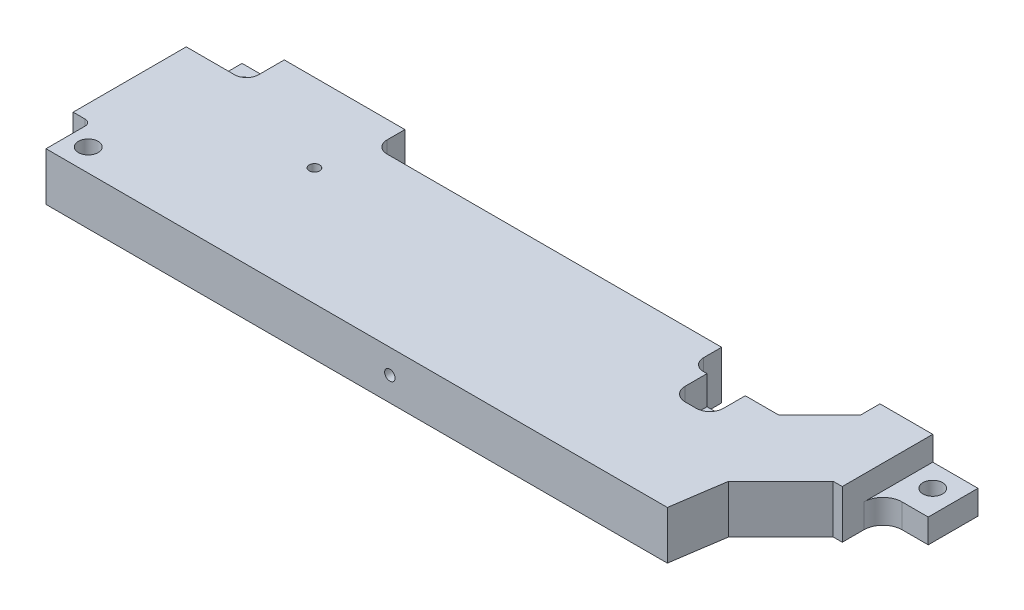
SolidWorks part; units mm, degrees
ref_plane "Front" through (0, 0, 0) normal (0, 0, 1) x (1, 0, 0)
ref_plane "Top" through (0, 0, 0) normal (0, 1, 0) x (1, 0, 0)
ref_plane "Right" through (0, 0, 0) normal (1, 0, 0) x (0, 0, -1)
sketch "Sketch1" plane through (0, 0, 0) normal (0, 0, 1) x (1, 0, 0)
  line L1 (-96.9906, 0) -> (106.1234, 0) construction
  line L2 (250, 8) -> (250, -8)
  line L3 (0, 8) -> (250, 8)
  line L4 (0, 8) -> (0, -8)
  line L5 (0, -8) -> (250, -8)
  dimension "D1" = 16
  dimension "D2" = 250
extrude "Base-Extrude" add sketch "Sketch1" along normal blind 65
sketch "Sketch3" plane through (0, 8, 0) normal (0, 1, 0) x (-1, 0, 0)
  line L0 (-250, 30) -> (-232, 30)
  line L1 (-250, 65) -> (-250, 0) construction
  line L2 (-214.6357, 47.3643) -> (-212, 65)
  line L3 (-250, 65) -> (0, 65) construction
  line L4 (-214.6357, 47.3643) -> (-232, 30)
  point P10 (-232, 30)
  dimension "D3" = 35
  dimension "D4" = 18
  dimension "D1" = 81.5
  dimension "D2" = 38
  dimension "D5" = 45
extrude "Access for Blade Clamp Bolts" cut sketch "Sketch3" against normal up to surface (15 mm away)
sketch "Sketch6" plane through (0, 8, 0) normal (0, 1, 0) x (-1, 0, 0)
  line L0 (0, -44.3876) -> (0, 104.5212) construction
  line L1 (-100, -18.9641) -> (-100, 23.8925) construction
  line L2 (-250, 0) -> (0, 0) construction
  line L3 (-60, 0) -> (-110, 0)
  line L4 (-60, 0) -> (-60, 6)
  line L5 (-64, 10) -> (-110, 10)
  line L6 (-110, 0) -> (-110, 10)
  line L7 (110, 0) -> (110, 6)
  line L8 (64, 10) -> (106, 10)
  line L9 (60, 0) -> (60, 6)
  line L10 (60, 0) -> (110, 0)
  arc A0 (-60, 6) -> (-64, 10) centre (-64, 6) ccw
  arc A2 (110, 6) -> (106, 10) centre (106, 6) ccw
  arc A3 (60, 6) -> (64, 10) centre (64, 6) cw
  point P12 (-100, 10)
  point P17 (100, 0)
  point P18 (100, 10)
  point P20 (-60, 10)
  point P23 (-110, 10)
  point P26 (110, 10)
  point P29 (60, 10)
  dimension "D5" = 4
  dimension "D6" = 4
  dimension "D1" = 100
  dimension "D2" = 10
  dimension "D3" = 40
  dimension "D4" = 10
extrude "Cut-Extrude2" cut sketch "Sketch6" against normal through all
sketch "Sketch7" plane through (0, 8, 0) normal (0, 1, 0) x (-1, 0, 0)
  line L0 (-250, 30) -> (-250, 0) construction
  line L1 (-217.5, 0) -> (-110, 0)
  line L2 (-217.5, 0) -> (-217.5, 5)
  line L3 (-175, 10) -> (-110, 10)
  line L4 (-110, 0) -> (-110, 10)
  line L5 (-250, 0) -> (-110, 0) construction
  line L6 (-175, 10) -> (-175, 16)
  line L7 (-179, 20) -> (-204, 20)
  line L8 (-217.5, 6.5) -> (-204, 20)
  line L10 (-217.5, 6.5) -> (-217.5, 5)
  arc A1 (-175, 16) -> (-179, 20) centre (-179, 16) ccw
  dimension "D2" = 29
  dimension "D4" = 4
  dimension "D1" = 32.5
  dimension "D3" = 10
  dimension "D5" = 42.5
  dimension "D6" = 45
  dimension "D7" = 5
extrude "Cut-Extrude3" cut sketch "Sketch7" against normal through all
hole_wizard "1/4 Clearance Hole1" positions "3DSketch2" profile "Sketch10" hole size "1/4" standard "Ansi Inch" end condition through all
sketch3d "3DSketch2"
  line L0 (250, 8, 30) -> (250, 8, 0) construction
  line L1 (250, 8, 0) -> (217.5, 8, 0) construction
  line L2 (0, 8, 65) -> (0, 8, 0) construction
  line L3 (60, 8, 0) -> (0, 8, 0) construction
  line L4 (212, 8, 65) -> (0, 8, 65) construction
  line L5 (250, 8, 30) -> (232, 8, 30) construction
  line L6 (250, 8, 30) -> (250, 8, 0) construction
  point P0 (242.5, 8, 22.5)
  point P1 (12.5, 8, 57.5)
  point P2 (12.5, 8, 6)
  point P5 (242.5, 8, 7.5)
  dimension "D1" = 7.5
  dimension "D2" = 7.5
  dimension "D7" = 7.5
  dimension "D3" = 12.5
  dimension "D4" = 12.5
  dimension "D5" = 6
  dimension "D6" = 7.5
  dimension "D8" = 7.5
sketch "Sketch10" plane through (242.5, 8, 22.5) normal (1, 0, 0) x (0, 0, 1)
  line L0 (0, 0) -> (0, 16)
  line L1 (0, 16) -> (3.2639, 16)
  line L2 (3.2639, 16) -> (3.2639, 0)
  line L5 (3.2639, 0) -> (0, 0)
  line L11 (0, -6.35) -> (0, 107.95) construction
  dimension "Thru Hole Dia." = 6.5278
  dimension "Thru Hole Depth" = 16
sketch "Sketch11" plane through (0, 8, 0) normal (0, 1, 0) x (-1, 0, 0)
  line L0 (0, 65) -> (0, 50)
  line L1 (0, 0) -> (-6, 0)
  line L2 (0, 0) -> (0, 12.5)
  line L3 (0, 12.5) -> (-4, 12.5)
  line L4 (-6, 0) -> (-6, 10.5)
  line L5 (0, 65) -> (0, 0) construction
  line L6 (0, 50) -> (-4, 50)
  line L7 (-6, 52) -> (-6, 65)
  line L8 (-212, 65) -> (0, 65) construction
  line L9 (-6, 65) -> (0, 65)
  arc A0 (-6, 10.5) -> (-4, 12.5) centre (-4, 10.5) cw
  arc A1 (-6, 52) -> (-4, 50) centre (-4, 52) ccw
  point P6 (-6, 12.5)
  dimension "D3" = 2
  dimension "D4" = 2
  dimension "D1" = 6
  dimension "D2" = 12.5
  dimension "D5" = 6
  dimension "D6" = 15
extrude "Cut-Extrude4" cut sketch "Sketch11" against normal through all
sketch "Sketch12" plane through (0, 8, 0) normal (0, 1, 0) x (-1, 0, 0)
  line L0 (0, 0) -> (-20, 0)
  line L1 (-60, 0) -> (-6, 0) construction
  line L2 (-20, 0) -> (-20, 8.5)
  line L3 (-16, 12.5) -> (0, 12.5)
  line L4 (0, 12.5) -> (0, 0)
  arc A0 (-20, 8.5) -> (-16, 12.5) centre (-16, 8.5) cw
  dimension "D2" = 4
  dimension "D1" = 20
extrude "Cut-Extrude5" cut sketch "Sketch12" against normal blind 8
hole_wizard "#8-32 Tapped Hole1" positions "3DSketch3" profile "Sketch13" tap size "#8-32" standard "Ansi Inch" end condition through all
sketch3d "3DSketch3"
  line L0 (212, 8, 65) -> (6, 8, 65) construction
  line L1 (250, 8, 30) -> (250, 8, 0) construction
  point P0 (56, 8, 26)
  dimension "D1" = 39
  dimension "D2" = 194
sketch "Sketch13" plane through (56, 8, 26) normal (1, 0, 0) x (0, 0, 1)
  line L0 (0, 0) -> (0, 16)
  line L1 (0, 16) -> (1.7272, 16)
  line L2 (1.7272, 16) -> (1.7272, 0)
  line L5 (1.7272, 0) -> (0, 0)
  line L11 (0, -6.35) -> (0, 107.95) construction
  dimension "Thru Tap Drill Dia." = 3.4544
  dimension "Thru Tap Drill Depth" = 16
cosmetic thread "Cosmetic Thread1" parameters "D1"=8.3312, "D2"=4.1656
hole_wizard "#8-32 Tapped Hole2" positions "Sketch15" profile "Sketch14" tap size "#8-32" standard "Ansi Inch"
sketch "Sketch15" plane through (0, 0, 65) normal (0, 0, 1) x (1, 0, 0)
  line L0 (250, 8) -> (250, -8) construction
  line L1 (6, -8) -> (212, -8) construction
  point P0 (120, 0)
  dimension "D1" = 130
  dimension "D2" = 8
sketch "Sketch14" plane through (120, 0, 65) normal (1, 0, 0) x (0, -1, 0)
  line L0 (0, 0) -> (0, 13.3314)
  line L1 (0, 13.3314) -> (1.7272, 12.2936)
  line L2 (1.7272, 12.2936) -> (1.7272, 0)
  line L5 (1.7272, 0) -> (0, 0)
  line L10 (0, 13.3314) -> (-1.7272, 12.2936) construction
  line L11 (0, -6.35) -> (0, 107.95) construction
  dimension "Tap Drill Dia." = 3.4544
  dimension "Tap Drill Depth" = 12.2936
  dimension "Drill Angle" = 118
cosmetic thread "Cosmetic Thread2" parameters "D1"=8.3312, "D2"=4.1656
hole_wizard "#8-32 Tapped Hole3" positions "Sketch18" profile "Sketch19" tap size "#8-32" standard "Ansi Inch" end condition through all
sketch "Sketch18" plane through (0, 8, 0) normal (0, 1, 0) x (-1, 0, 0)
  line L0 (-212, 65) -> (-6, 65) construction
  line L1 (-250, 30) -> (-250, 0) construction
  point P0 (-186.5, 26.9)
  dimension "D1" = 38.1
  dimension "D2" = 63.5
sketch "Sketch19" plane through (186.5, 8, 26.9) normal (1, 0, 0) x (0, 0, 1)
  line L0 (0, 0) -> (0, 16)
  line L1 (0, 16) -> (1.7272, 16)
  line L2 (1.7272, 16) -> (1.7272, 0)
  line L5 (1.7272, 0) -> (0, 0)
  line L11 (0, -6.35) -> (0, 107.95) construction
  dimension "Thru Tap Drill Dia." = 3.4544
  dimension "Thru Tap Drill Depth" = 16
cosmetic thread "Cosmetic Thread3" parameters "D1"=8.3312, "D2"=4.1656
sketch "Sketch20" plane through (0, 8, 0) normal (0, 1, 0) x (-1, 0, 0)
  line L0 (-250, 30) -> (-232, 30) construction
  line L1 (-250, 0) -> (-235, 0)
  line L2 (-250, 0) -> (-250, 30)
  line L3 (-250, 30) -> (-235, 30)
  line L4 (-235, 0) -> (-235, 30)
  dimension "D1" = 15
extrude "Cut-Extrude6" cut sketch "Sketch20" against normal up to surface (8 mm away) up to face at (12.2071, 0, 7.5404)
sketch "Sketch22" plane through (0, 8, 0) normal (0, 1, 0) x (-1, 0, 0)
  line L0 (-179, 20) -> (-204, 20) construction
  line L1 (-180.15, 20) -> (-192.85, 20)
  line L2 (-180.15, 20) -> (-180.15, 31.75)
  line L3 (-180.15, 31.75) -> (-192.85, 31.75)
  line L4 (-192.85, 20) -> (-192.85, 31.75)
  circle A0 centre (-186.5, 26.9) radius 1.7272 construction
  dimension "D1" = 6.35
  dimension "D2" = 12.7
  dimension "D3" = 4.85
extrude "Cut-Extrude8" cut sketch "Sketch22" against normal blind 9.525
sketch "Sketch23" plane through (0, 0, 0) normal (0, 1, 0) x (-1, 0, 0)
  line L0 (-241.35, 16.5) -> (-250, 16.5)
  line L1 (-235, 0) -> (-235, 30) construction
  line L2 (-250, 30) -> (-250, 0) construction
  line L3 (-235, 22.85) -> (-235, 30)
  line L4 (-235, 30) -> (-250, 30)
  line L5 (-250, 30) -> (-250, 16.5)
  circle A0 centre (-242.5, 22.5) radius 6 construction
  arc A1 (-241.35, 16.5) -> (-235, 22.85) centre (-241.35, 22.85) ccw
  point P15 (-235, 16.5)
  dimension "D1" = 12
  dimension "D2" = 6.35
extrude "Cut-Extrude9" cut sketch "Sketch23" against normal through all
fillet "Fillet1" radius 4.5 2 edges at (180.15, 3.2375, 31.75) (192.85, 3.2375, 31.75)
